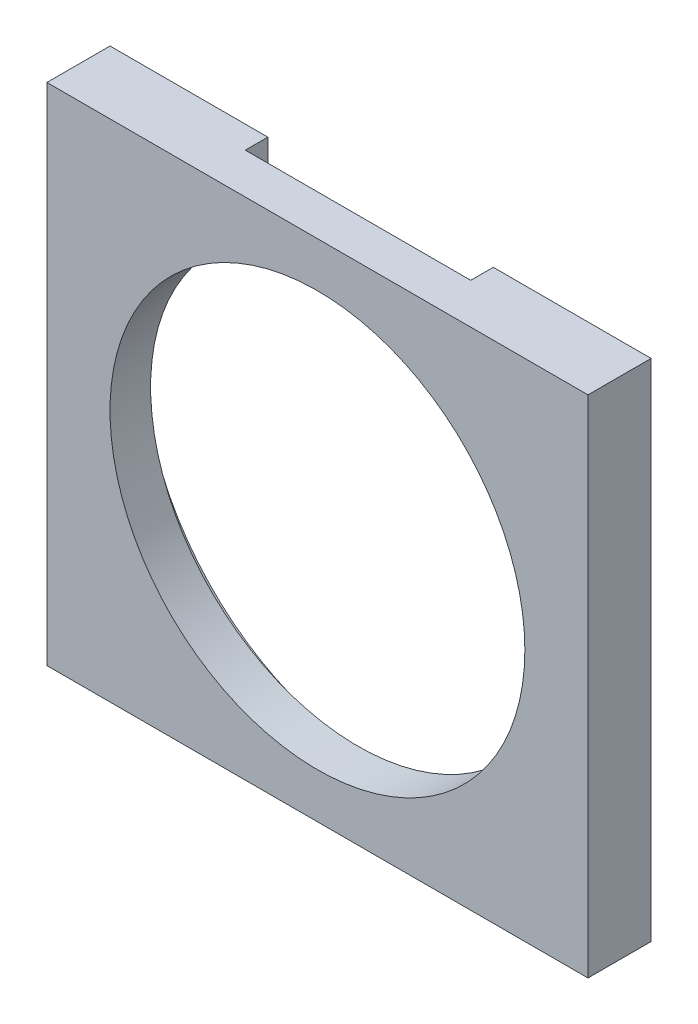
SolidWorks part; units mm, degrees
ref_plane "Front Plane" through (0, 0, 0) normal (0, 0, 1) x (1, 0, 0)
ref_plane "Top Plane" through (0, 0, 0) normal (0, 1, 0) x (1, 0, 0)
ref_plane "Right Plane" through (0, 0, 0) normal (1, 0, 0) x (0, 0, -1)
sketch "Sketch1" plane through (0, 0, 0) normal (0, 0, 1) x (1, 0, 0)
  line L1 (-76.2, 71.12) -> (76.2, 71.12)
  line L2 (-76.2, 71.12) -> (-76.2, -71.12)
  line L3 (-76.2, -71.12) -> (76.2, -71.12)
  line L4 (76.2, 71.12) -> (76.2, -71.12)
  line L5 (-76.2, 71.12) -> (76.2, -71.12) construction
  line L6 (-76.2, -71.12) -> (76.2, 71.12) construction
  line L7 (-31.75, 71.12) -> (31.75, 71.12)
  line L8 (-31.75, 71.12) -> (-31.75, 58.6301)
  line L10 (31.75, 71.12) -> (31.75, 58.6301)
  arc A0 (-31.75, 58.6301) -> (31.75, 58.6301) centre (0, 0) ccw
  point P0 (0, 0)
  point P12 (31.75, 58.6301)
  point P13 (-31.75, 58.6301)
  dimension "D3" = 133.35
  dimension "D1" = 152.4
  dimension "D2" = 142.24
  dimension "D4" = 44.45
  dimension "D5" = 63.5
extrude "Boss-Extrude1" add sketch "Sketch1" along normal blind 6.35 contours A0 L8 L1 L2 L3 L4 L10
sketch "Sketch2" plane through (0, 0, 6.35) normal (0, 0, 1) x (1, 0, 0)
  line L1 (-76.2, 71.12) -> (76.2, 71.12)
  line L2 (-76.2, 71.12) -> (-76.2, -71.12)
  line L3 (-76.2, -71.12) -> (76.2, -71.12)
  line L4 (76.2, 71.12) -> (76.2, -71.12)
  circle A0 centre (0, 0) radius 58.42
  dimension "D1" = 116.84
extrude "Boss-Extrude2" add sketch "Sketch2" along normal blind 11.43
